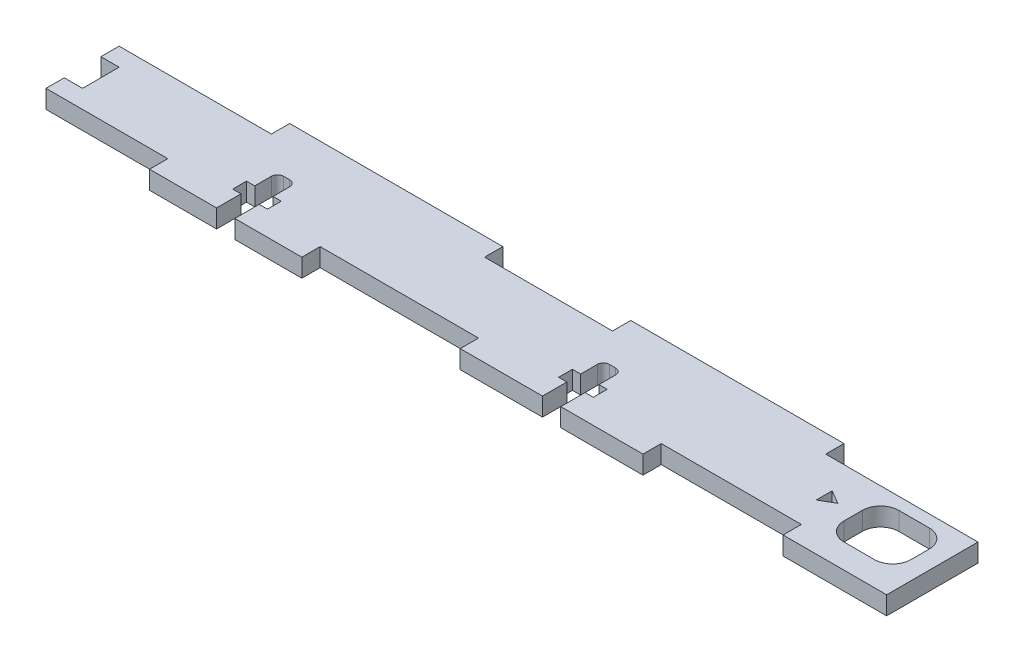
SolidWorks part; units mm, degrees
material "Acrylic (Medium-high impact)"
ref_plane "Plano frontal" through (0, 0, 0) normal (0, 0, 1) x (1, 0, 0)
ref_plane "Plano superior" through (0, 0, 0) normal (0, 1, 0) x (1, 0, 0)
ref_plane "Plano direito" through (0, 0, 0) normal (1, 0, 0) x (0, 0, -1)
sketch "Sketch1" plane through (0, 0, 0) normal (0, 1, 0) x (1, 0, 0)
  line L1 (-70.5, 6) -> (70.5, 6)
  line L2 (-70.5, 6) -> (-70.5, -6)
  line L3 (-70.5, -6) -> (70.5, -6)
  line L4 (70.5, 6) -> (70.5, -6)
  point P4 (0, 6)
  point P6 (-70.5, 0)
  dimension "D1" = 141
  dimension "D2" = 12
extrude "Boss-Extrude1" add sketch "Sketch1" along normal mid plane 3
sketch "Sketch2" plane through (0, 0, 0) normal (0, 1, 0) x (1, 0, 0)
  line L0 (-70.5, 6) -> (-70.5, -6) construction
  line L5 (-70.5, -6) -> (70.5, -6) construction
  line L6 (0.5, -6) -> (30.5, -6)
  line L7 (0.5, -6) -> (0.5, -9)
  line L8 (0.5, -9) -> (30.5, -9)
  line L9 (30.5, -6) -> (30.5, -9)
  line L10 (70.5, -6) -> (70.5, 6) construction
  line L18 (70.5, -6) -> (53.5, -6)
  line L19 (70.5, -6) -> (70.5, -9)
  line L20 (70.5, -9) -> (53.5, -9)
  line L21 (53.5, -6) -> (53.5, -9)
  dimension "D1" = 3
  dimension "D2" = 30
  dimension "D3" = 71
  dimension "D4" = 23
extrude "Boss-Extrude2" add sketch "Sketch2" along normal mid plane 3
sketch "Sketch12" plane through (0, 0, 0) normal (0, 1, 0) x (1, 0, 0)
  line L0 (-70.5, -6) -> (0.5, -6) construction
  line L1 (-50.5, -6) -> (-25.5, -6)
  line L2 (-50.5, -6) -> (-50.5, -9)
  line L3 (-50.5, -9) -> (-25.5, -9)
  line L4 (-25.5, -6) -> (-25.5, -9)
  line L5 (0.5, -9) -> (30.5, -9) construction
  line L6 (-5.5, 6) -> (-5.5, -6) construction
  line L7 (70.5, 6) -> (-70.5, 6) construction
  line L8 (-70.5, 6) -> (-70.5, -6) construction
  line L9 (-5.5, 6) -> (-70.5, 6) construction
  line L10 (-38, 6) -> (-38, -6) construction
  point P18 (-38, -6)
  dimension "D2" = 25
  dimension "D3" = 20
  dimension "D4" = 20
extrude "Boss-Extrude3" add sketch "Sketch12" along normal mid plane 3
sketch "Sketch11" plane through (0, 0, 0) normal (0, 1, 0) x (1, 0, 0)
  line L0 (-50.5, -9) -> (-25.5, -9) construction
  line L5 (-39.5, -2.73) -> (-39.5, 0)
  line L6 (-36.5, -2.73) -> (-35.15, -2.73)
  line L15 (0.5, -9) -> (30.5, -9) construction
  line L16 (14, -9) -> (17, -9)
  line L17 (14, -9) -> (14, -5)
  line L18 (15, 1) -> (16, 1)
  line L19 (17, -9) -> (17, -5)
  line L20 (0.5, -9) -> (30.5, -9) construction
  line L21 (14, -2.73) -> (14, 0)
  line L22 (12.65, -2.73) -> (14, -2.73)
  line L23 (12.65, -2.73) -> (12.65, -5)
  line L24 (12.65, -5) -> (14, -5)
  line L25 (18.35, -2.73) -> (18.35, -5)
  line L26 (17, -2.73) -> (18.35, -2.73)
  line L27 (17, -2.73) -> (17, 0)
  line L28 (17, -5) -> (18.35, -5)
  line L29 (-36.5, -5) -> (-35.15, -5)
  line L34 (-36.5, -2.73) -> (-36.5, 0)
  line L44 (-39.5, -9) -> (-36.5, -9)
  line L45 (-39.5, -9) -> (-39.5, -5)
  line L46 (-38.5, 1) -> (-37.5, 1)
  line L47 (-36.5, -9) -> (-36.5, -5)
  line L48 (-50.5, -6) -> (-50.5, -9) construction
  line L49 (-25.5, -9) -> (-25.5, -6) construction
  line L51 (-40.85, -2.73) -> (-39.5, -2.73)
  line L52 (-40.85, -2.73) -> (-40.85, -5)
  line L53 (-40.85, -5) -> (-39.5, -5)
  line L54 (-35.15, -2.73) -> (-35.15, -5)
  arc A2 (16, 1) -> (17, 0) centre (16, 0) cw
  arc A3 (14, 0) -> (15, 1) centre (15, 0) cw
  arc A4 (-37.5, 1) -> (-36.5, 0) centre (-37.5, 0) cw
  arc A5 (-39.5, 0) -> (-38.5, 1) centre (-38.5, 0) cw
  point P20 (-36.5, 1)
  point P23 (-39.5, 1)
  point P34 (15.5, -9)
  point P45 (17, 1)
  point P48 (14, 1)
  dimension "D16" = 1
  dimension "D8" = 1
  dimension "D2" = 3
  dimension "D3" = 11
  dimension "D4" = 11
  dimension "D5" = 2.27
  dimension "D6" = 1.35
  dimension "D7" = 1.35
  dimension "D10" = 3
  dimension "D11" = 10
  dimension "D12" = 1.35
  dimension "D13" = 1.35
  dimension "D14" = 4
  dimension "D15" = 2.27
extrude "Cut-Extrude8" cut sketch "Sketch11" against normal through all both and the other way through all
sketch "Sketch13" plane through (0, 0, 0) normal (0, 1, 0) x (1, 0, 0)
  line L10 (70.5, 6) -> (-70.5, 6) construction
  line L12 (-45.5, 6) -> (-10.5, 6)
  line L13 (-45.5, 6) -> (-45.5, 9)
  line L14 (-45.5, 9) -> (-10.5, 9)
  line L15 (-10.5, 6) -> (-10.5, 9)
  line L16 (70.5, -9) -> (70.5, 6) construction
  line L17 (10.5, 6) -> (45.5, 6)
  line L18 (10.5, 6) -> (10.5, 9)
  line L19 (10.5, 9) -> (45.5, 9)
  line L20 (45.5, 6) -> (45.5, 9)
  dimension "D1" = 35
  dimension "D2" = 3
  dimension "D3" = 25
  dimension "D4" = 21
extrude "Boss-Extrude4" add sketch "Sketch13" along normal mid plane 3
sketch "Sketch15" plane through (0, 0, 0) normal (0, 1, 0) x (1, 0, 0)
  line L1 (56.5, 4) -> (67.5, 4)
  line L2 (56.5, 4) -> (56.5, -5)
  line L3 (56.5, -5) -> (67.5, -5)
  line L4 (67.5, 4) -> (67.5, -5)
  line L6 (70.5, 6) -> (45.5, 6) construction
  line L7 (70.5, -9) -> (70.5, 6) construction
  dimension "D4" = 9
  dimension "D2" = 11
  dimension "D3" = 2
  dimension "D5" = 3
extrude "Cut-Extrude10" cut sketch "Sketch15" against normal through all both and the other way through all
fillet "Fillet4" radius 3 4 edges at (56.5, 0, -4) (67.5, 0, -4) (67.5, 0, 5) (56.5, 0, 5)
sketch "Sketch16" plane through (0, 0, 0) normal (0, 1, 0) x (1, 0, 0)
  line L0 (70.5, -9) -> (70.5, 6) construction
  line L4 (53.5, 0) -> (51.25, 1.299)
  line L5 (51.25, 1.299) -> (51.25, -1.299)
  line L6 (51.25, -1.299) -> (53.5, 0)
  line L7 (56.5, 1) -> (56.5, -2) construction
  circle A0 centre (52, 0) radius 1.5 construction
  dimension "D1" = 3
  dimension "D2" = 3
extrude "Cut-Extrude11" cut sketch "Sketch16" against normal through all both and the other way through all
sketch "Sketch17" plane through (0, 0, 0) normal (0, 1, 0) x (1, 0, 0)
  line L0 (-70.5, 6) -> (-70.5, -6) construction
  line L1 (-70.5, 3) -> (-67.5, 3)
  line L2 (-70.5, 3) -> (-70.5, -3)
  line L3 (-70.5, -3) -> (-67.5, -3)
  line L4 (-67.5, 3) -> (-67.5, -3)
  point P6 (-67.5, 0)
  dimension "D1" = 3
  dimension "D2" = 6
extrude "Cut-Extrude12" cut sketch "Sketch17" against normal through all both and the other way through all
